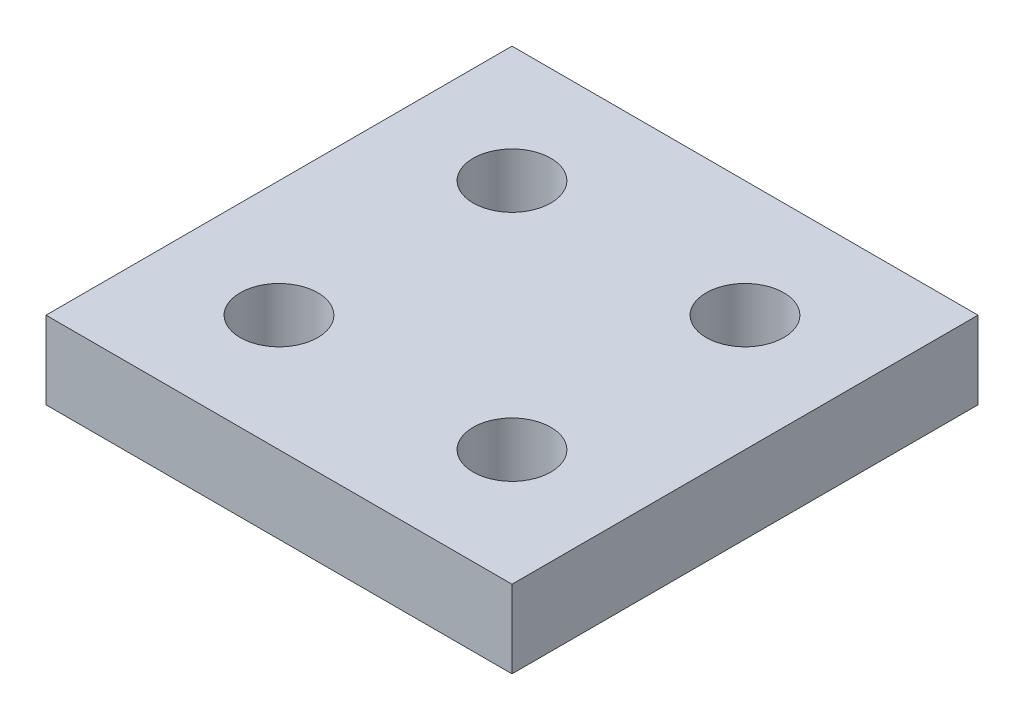
SolidWorks part; units mm, degrees
ref_plane "Front Plane" through (0, 0, 0) normal (0, 0, 1) x (1, 0, 0)
ref_plane "Top Plane" through (0, 0, 0) normal (0, 1, 0) x (1, 0, 0)
ref_plane "Right Plane" through (0, 0, 0) normal (1, 0, 0) x (0, 0, -1)
sketch "Sketch1" plane through (0, 0, 0) normal (0, 1, 0) x (1, 0, 0)
  line L1 (0, 0) -> (60, 0)
  line L2 (0, 0) -> (0, 60)
  line L3 (0, 60) -> (60, 60)
  line L4 (60, 0) -> (60, 60)
  dimension "D1" = 60
  dimension "D2" = 60
extrude "Boss-Extrude1" add sketch "Sketch1" along normal blind 10
sketch "Sketch2" plane through (0, 10, 0) normal (0, 1, 0) x (1, 0, 0)
  line L0 (0, 0) -> (60, 0) construction
  line L1 (0, 60) -> (0, 0) construction
  circle A0 centre (15, 15) radius 5
  dimension "D1" = 15
  dimension "D2" = 15
  dimension "D3" = 10
extrude "Cut-Extrude1" cut sketch "Sketch2" against normal through all
pattern_linear "LPattern1" count 4 spacing 30 along (1, 0, 0) count 4 spacing 30 along (0, 0, -1) of "Cut-Extrude1"
